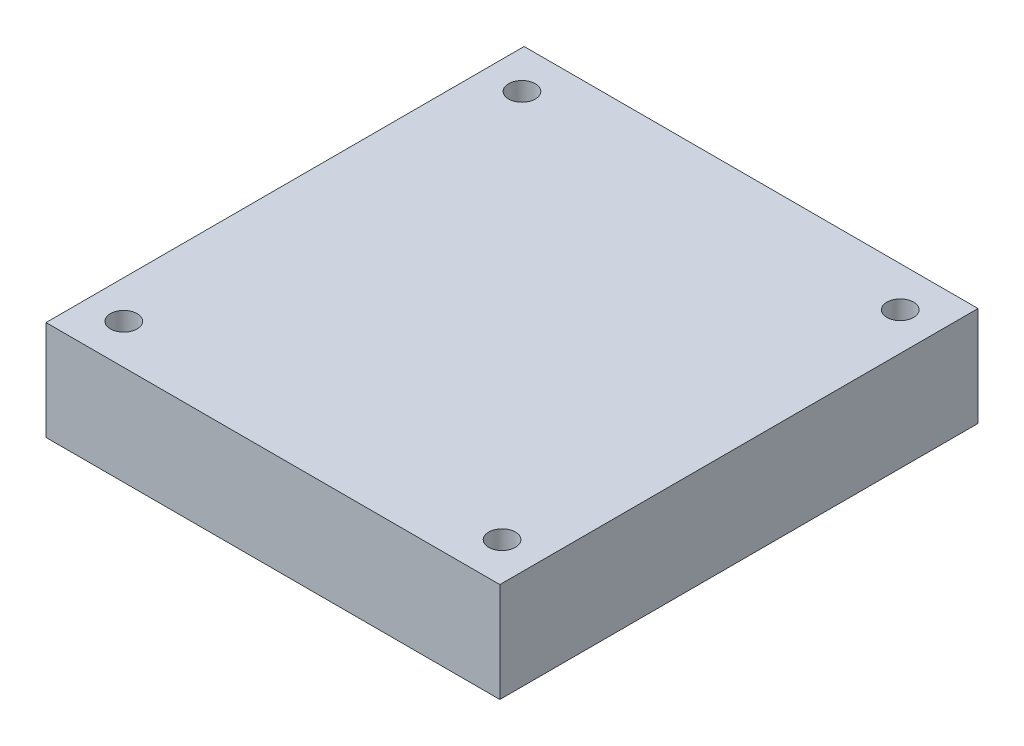
SolidWorks part; units mm, degrees
ref_plane "Front Plane" through (0, 0, 0) normal (0, 0, 1) x (1, 0, 0)
ref_plane "Top Plane" through (0, 0, 0) normal (0, 1, 0) x (1, 0, 0)
ref_plane "Right Plane" through (0, 0, 0) normal (1, 0, 0) x (0, 0, -1)
sketch "Sketch1" plane through (0, 0, 0) normal (0, 1, 0) x (1, 0, 0)
  line L1 (-28.95, 30.5) -> (28.95, 30.5)
  line L2 (-28.95, 30.5) -> (-28.95, -30.5)
  line L3 (-28.95, -30.5) -> (28.95, -30.5)
  line L4 (28.95, 30.5) -> (28.95, -30.5)
  dimension "D1" = 28.95
  dimension "D2" = 57.9
  dimension "D3" = 30.5
  dimension "D4" = 61
extrude "Extrude1" add sketch "Sketch1" along normal blind 12.7
sketch "Sketch10" plane through (0, 0, 0) normal (0, -1, 0) x (1, 0, 0)
  line L0 (-28.95, 30.5) -> (28.95, 30.5) construction
  line L1 (28.95, 30.5) -> (28.95, -30.5) construction
  line L2 (-28.95, 30.5) -> (28.95, 30.5) construction
  line L4 (-28.95, -30.5) -> (-28.95, 30.5) construction
  line L6 (28.95, -30.5) -> (-28.95, -30.5) construction
  line L7 (28.95, 30.5) -> (28.95, -30.5) construction
  circle A0 centre (24.13, 25.4) radius 1.7
  circle A1 centre (-24.13, 25.4) radius 1.7
  circle A2 centre (-24.13, -25.4) radius 1.7
  circle A3 centre (24.13, -25.4) radius 1.7
  dimension "D1" = 5.1
  dimension "D3" = 5.1
  dimension "D2" = 4.82
  dimension "D4" = 4.82
  dimension "D5" = 5.1
  dimension "D6" = 4.82
  dimension "D7" = 5.1
  dimension "D8" = 4.82
  dimension "D9" = 50.8
  dimension "D10" = 48.26
hole_wizard "M3 Clearance Hole1" positions "3DSketch2" profile "Sketch12" hole size "M3" standard "Ansi Metric"
sketch3d "3DSketch2"
  point P0 (24.13, 0, -25.4)
  point P3 (-24.13, 0, -25.4)
  point P6 (-24.13, 0, 25.4)
  point P9 (24.13, 0, 25.4)
sketch "Sketch12" plane through (24.13, 0, -25.4) normal (1, 0, 0) x (0, 0, -1)
  line L0 (0, 0) -> (0, 13.7215)
  line L1 (0, 13.7215) -> (1.7, 12.7)
  line L2 (1.7, 12.7) -> (1.7, 0)
  line L5 (1.7, 0) -> (0, 0)
  line L10 (0, 13.7215) -> (-1.7, 12.7) construction
  line L11 (0, -6.35) -> (0, 107.95) construction
  dimension "Hole Dia." = 3.4
  dimension "Hole Depth" = 12.7
  dimension "Drill Angle" = 118
sketch "Sketch13" plane through (0, 12.7, 0) normal (0, 1, 0) x (-1, 0, 0)
  line L0 (0, -30.5) -> (0, 30.5) construction
  line L1 (-28.95, -30.5) -> (28.95, -30.5) construction
  line L2 (28.95, 30.5) -> (-28.95, 30.5) construction
  line L3 (28.95, 0) -> (-28.95, 0) construction
  line L4 (28.95, -30.5) -> (28.95, 30.5) construction
  line L5 (-28.95, 30.5) -> (-28.95, -30.5) construction
